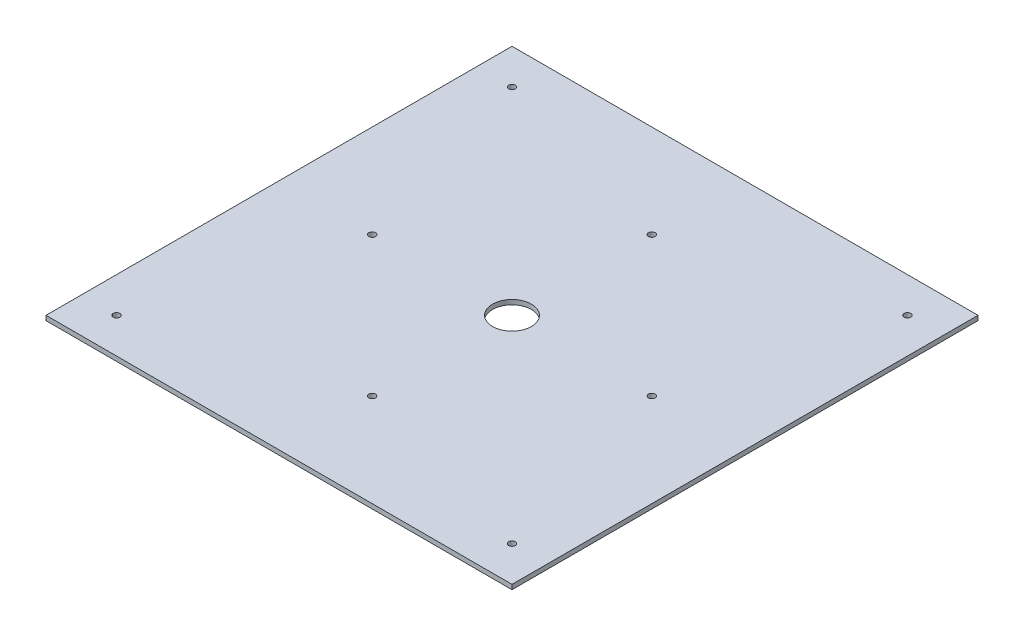
SolidWorks part; units mm, degrees
ref_plane "前视基准面" through (0, 0, 0) normal (0, 0, 1) x (1, 0, 0)
ref_plane "上视基准面" through (0, 0, 0) normal (0, 1, 0) x (1, 0, 0)
ref_plane "右视基准面" through (0, 0, 0) normal (1, 0, 0) x (0, 0, -1)
sketch "草图1" plane through (0, 0, 0) normal (0, 1, 0) x (1, 0, 0)
  line L0 (0, 150) -> (452.0299, 150) construction
  line L1 (0, 0) -> (300, 0)
  line L2 (0, 0) -> (0, 300)
  line L3 (0, 300) -> (300, 300)
  line L4 (300, 0) -> (300, 300)
  line L5 (150, 300) -> (150, -208.1919) construction
  line L6 (150, 150) -> (0, 300) construction
  circle A0 centre (150, 150) radius 12.5
  circle A1 centre (22.7208, 277.2792) radius 2.15
  circle A2 centre (277.2792, 277.2792) radius 2.15
  circle A3 centre (277.2792, 22.7208) radius 2.15
  circle A4 centre (22.7208, 22.7208) radius 2.15
  circle A5 centre (150, 240) radius 2.15
  circle A6 centre (240, 150) radius 2.15
  circle A7 centre (150, 60) radius 2.15
  circle A8 centre (60, 150) radius 2.15
  point P22 (150, 150)
  point P31 (150, 150)
  dimension "D3" = 25
  dimension "D4" = 4.3
  dimension "D5" = 180
  dimension "D7" = 90
  dimension "D8" = 4.3
  dimension "D1" = 300
  dimension "D2" = 300
  dimension "D6" = 4
  dimension "D9" = 4
extrude "凸台-拉伸1" add sketch "草图1" along normal blind 3
